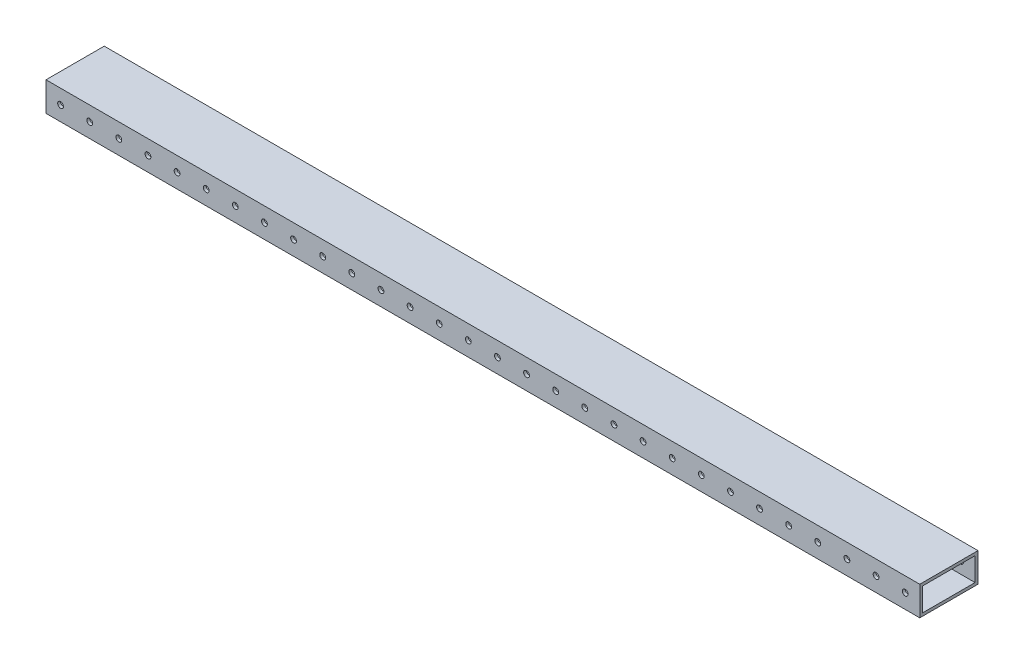
SolidWorks part; units mm, degrees
ref_plane "Front Plane" through (0, 0, 0) normal (0, 0, 1) x (1, 0, 0)
ref_plane "Top Plane" through (0, 0, 0) normal (0, 1, 0) x (1, 0, 0)
ref_plane "Right Plane" through (0, 0, 0) normal (1, 0, 0) x (0, 0, -1)
sketch "Sketch1" plane through (0, 0, 0) normal (1, 0, 0) x (0, 0, -1)
  line L0 (2.54, 2.54) -> (2.54, 22.86)
  line L1 (0, 0) -> (50.8, 0)
  line L2 (0, 0) -> (0, 25.4)
  line L3 (0, 25.4) -> (50.8, 25.4)
  line L4 (50.8, 0) -> (50.8, 25.4)
  line L5 (2.54, 22.86) -> (48.26, 22.86)
  line L6 (48.26, 2.54) -> (48.26, 22.86)
  line L7 (2.54, 2.54) -> (48.26, 2.54)
  dimension "D1" = 50.8
  dimension "D2" = 25.4
  dimension "D3" = 2.54
extrude "Boss-Extrude1" add sketch "Sketch1" along normal blind 762
sketch "Sketch2" plane through (0, 0, 0) normal (0, 0, 1) x (1, 0, 0)
  line L0 (0, 25.4) -> (0, 0) construction
  line L1 (762, 0) -> (0, 0) construction
  circle A0 centre (12.7, 12.7) radius 2.54
  dimension "D1" = 5.08
  dimension "D2" = 12.7
  dimension "D3" = 12.7
extrude "Cut-Extrude1" cut sketch "Sketch2" against normal through all
pattern_linear "LPattern1" count 30 spacing 25.4 along (1, 0, 0) of "Cut-Extrude1"
